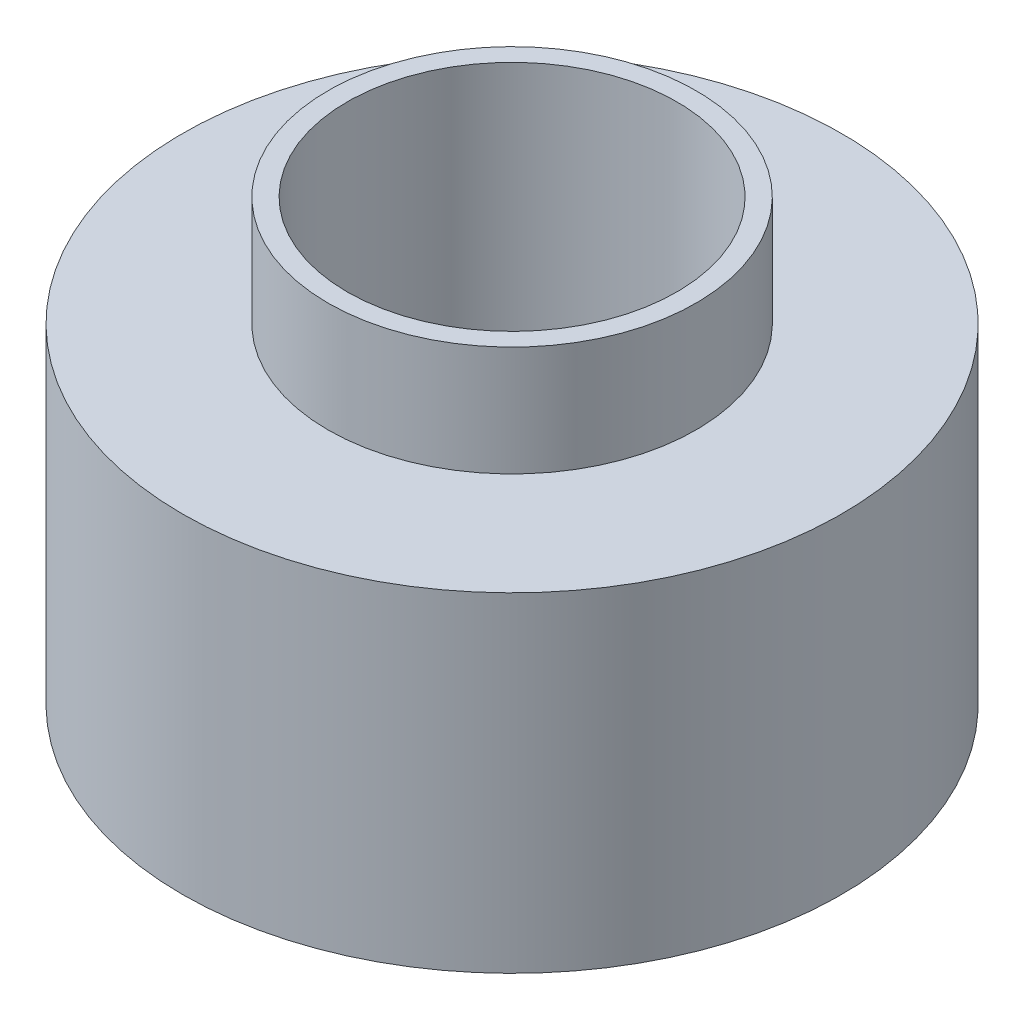
SolidWorks part; units mm, degrees
material "Plain Carbon Steel"
ref_plane "Front Plane" through (0, 0, 0) normal (0, 0, 1) x (1, 0, 0)
ref_plane "Top Plane" through (0, 0, 0) normal (0, 1, 0) x (1, 0, 0)
ref_plane "Right Plane" through (0, 0, 0) normal (1, 0, 0) x (0, 0, -1)
sketch "Sketch1" plane through (0, 0, 0) normal (0, 0, 1) x (1, 0, 0)
  line L0 (0, 75.7914) -> (0, -85.6225) construction
  line L1 (0, -55) -> (0, 55) construction
  line L2 (0, 12.7) -> (-5.3185, 12.7)
  line L3 (-5.3185, 12.7) -> (-5.3185, 9.525)
  line L4 (-5.3185, 9.525) -> (-9.525, 9.525)
  line L5 (-9.525, 9.525) -> (-9.525, 0)
  line L6 (55, 0) -> (-55, 0) construction
  line L7 (-9.525, 0) -> (0, 0)
  line L8 (0, 0) -> (0, 12.7)
  dimension "D1" = 9.525
  dimension "D2" = 9.525
  dimension "D3" = 3.175
revolve "Revolve1" add sketch "Sketch1" angle 360 about L0
sketch "Sketch2" plane through (0, 12.7, 0) normal (0, 1, 0) x (1, 0, 0)
  circle A0 centre (0, 0) radius 4.7625
  dimension "D1" = 9.525
extrude "Cut-Extrude1" cut sketch "Sketch2" against normal through all and the other way through all
